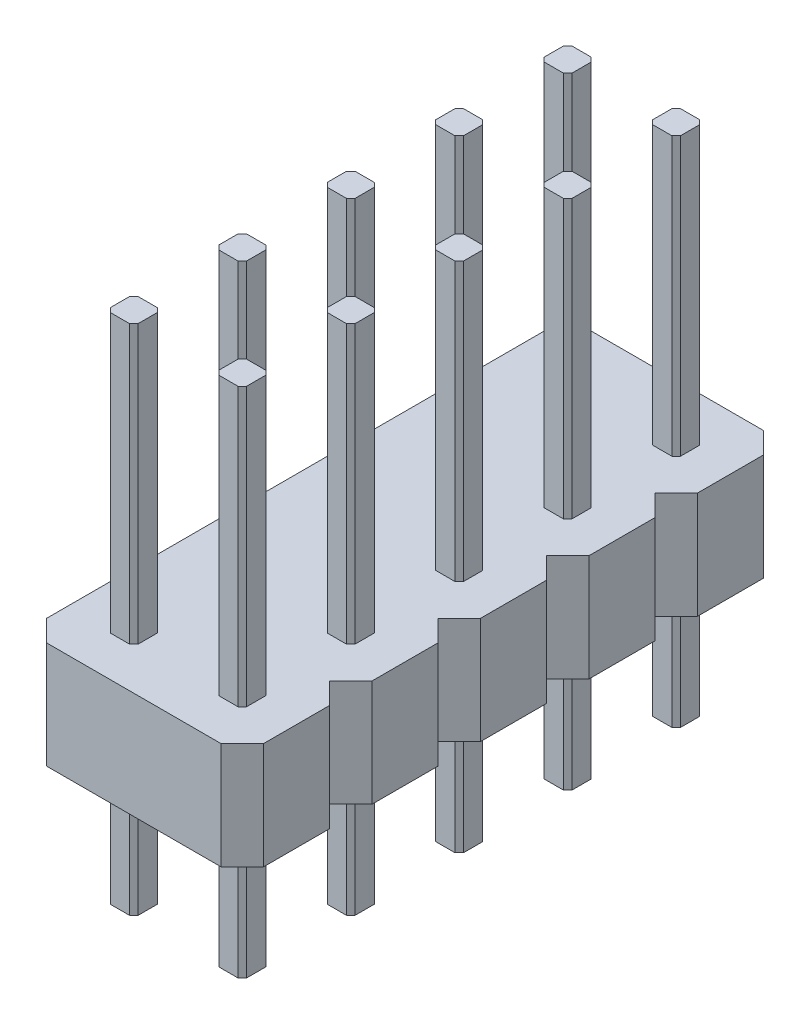
SolidWorks part; units mm, degrees
ref_plane "Front Plane" through (0, 0, 0) normal (0, 0, 1) x (1, 0, 0)
ref_plane "Top Plane" through (0, 0, 0) normal (0, 1, 0) x (1, 0, 0)
ref_plane "Right Plane" through (0, 0, 0) normal (1, 0, 0) x (0, 0, -1)
sketch "Sketch1" plane through (0, 0, 0) normal (0, 1, 0) x (1, 0, 0)
  line L0 (-0.325, -0.225) -> (-0.225, -0.325)
  line L1 (-0.225, 0.325) -> (0.225, 0.325)
  line L2 (-0.325, 0.225) -> (-0.325, -0.225)
  line L3 (-0.225, -0.325) -> (0.225, -0.325)
  line L4 (0.325, 0.225) -> (0.325, -0.225)
  line L5 (-0.325, 0.325) -> (0.325, -0.325) construction
  line L6 (-0.325, -0.325) -> (0.325, 0.325) construction
  line L7 (0.225, -0.325) -> (0.325, -0.225)
  line L8 (0.225, 0.325) -> (0.325, 0.225)
  line L9 (-0.325, 0.225) -> (-0.225, 0.325)
  point P0 (0, 0)
  dimension "D1" = 0.65
extrude "Boss-Extrude1" add sketch "Sketch1" along normal blind 12
pattern_linear "LPattern2" count 2 spacing 2.54 along (1, 0, 0) of bodies 101
ref_plane "Plane1" through (0, 3, 0) normal (0, -1, 0) x (-1, 0, 0)
sketch "Sketch2" plane through (0, 3, 0) normal (0, -1, 0) x (-1, 0, 0)
  line L0 (0.325, 0) -> (-2.865, 0) construction
  line L1 (0.325, 0.225) -> (0.325, -0.225) construction
  line L2 (-2.865, -0.225) -> (-2.865, 0.225) construction
  line L3 (-3.81, 0.77) -> (-3.31, 1.27)
  line L4 (-3.31, 1.27) -> (0.77, 1.27)
  line L5 (-3.81, 0.77) -> (-3.81, -0.77)
  line L6 (-3.31, -1.27) -> (0.77, -1.27)
  line L7 (1.27, 0.77) -> (1.27, -0.77)
  line L8 (-3.81, 1.27) -> (1.27, -1.27) construction
  line L9 (-3.81, -1.27) -> (1.27, 1.27) construction
  line L10 (-3.81, -0.77) -> (-3.31, -1.27)
  line L11 (0.77, -1.27) -> (1.27, -0.77)
  line L12 (0.77, 1.27) -> (1.27, 0.77)
  point P6 (-1.27, 0)
  dimension "D1" = 5.08
  dimension "D2" = 2.54
extrude "Boss-Extrude2" add sketch "Sketch2" against normal blind 2.5
pattern_linear "LPattern3" count 5 spacing 2.54 along (0, 0, -1) of bodies 104
combine bodies "Combine1" operation type add bodies to combine 104 105 106 107 108
